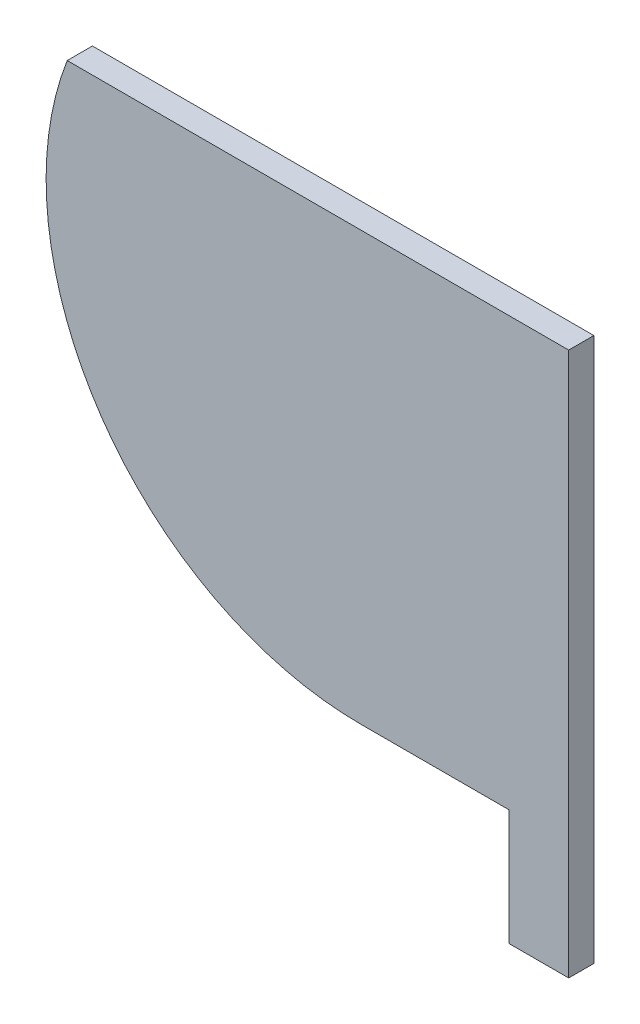
SolidWorks part; units mm, degrees
ref_plane "Front Plane" through (0, 0, 0) normal (0, 0, 1) x (1, 0, 0)
ref_plane "Top Plane" through (0, 0, 0) normal (0, 1, 0) x (1, 0, 0)
ref_plane "Right Plane" through (0, 0, 0) normal (1, 0, 0) x (0, 0, -1)
sketch "Sketch1" plane through (0, 0, 0) normal (0, 0, 1) x (1, 0, 0)
  line L12 (0, 0) -> (0, -85)
  line L13 (-41.2806, -85) -> (0, -85)
  line L14 (0, 0) -> (-99.5901, 0)
  arc A3 (-99.5901, 0) -> (-41.2806, -85) centre (-41.2806, -22.5) ccw
  dimension "D1" = 62.5
  dimension "D2" = 41.2806
  dimension "D3" = 85
extrude "Boss-Extrude1" add sketch "Sketch1" along normal blind 5
sketch "Sketch2" plane through (0, 0, 5) normal (0, 0, 1) x (1, 0, 0)
  line L0 (-11.8802, -85) -> (-11.8802, -108)
  line L1 (-11.8802, -85) -> (0, -85)
  line L2 (-11.8802, -108) -> (0, -108)
  line L3 (0, -85) -> (0, -108)
  line L5 (5.3398, -108) -> (-16.1602, -108) construction
  line L8 (-41.2806, -85) -> (0, -85) construction
  line L12 (6.3398, -87.011) -> (6.3398, -110.6927) construction
  line L13 (6.3398, -108) -> (6.3398, -103) construction
  line L14 (-12.8802, -88.5135) -> (-12.8802, -110.6927) construction
  line L15 (-12.8802, -103) -> (-12.8802, -108) construction
  line L17 (0, -85) -> (0, 0) construction
  dimension "D1" = 1
extrude "Boss-Extrude2" add sketch "Sketch2" against normal blind 5
